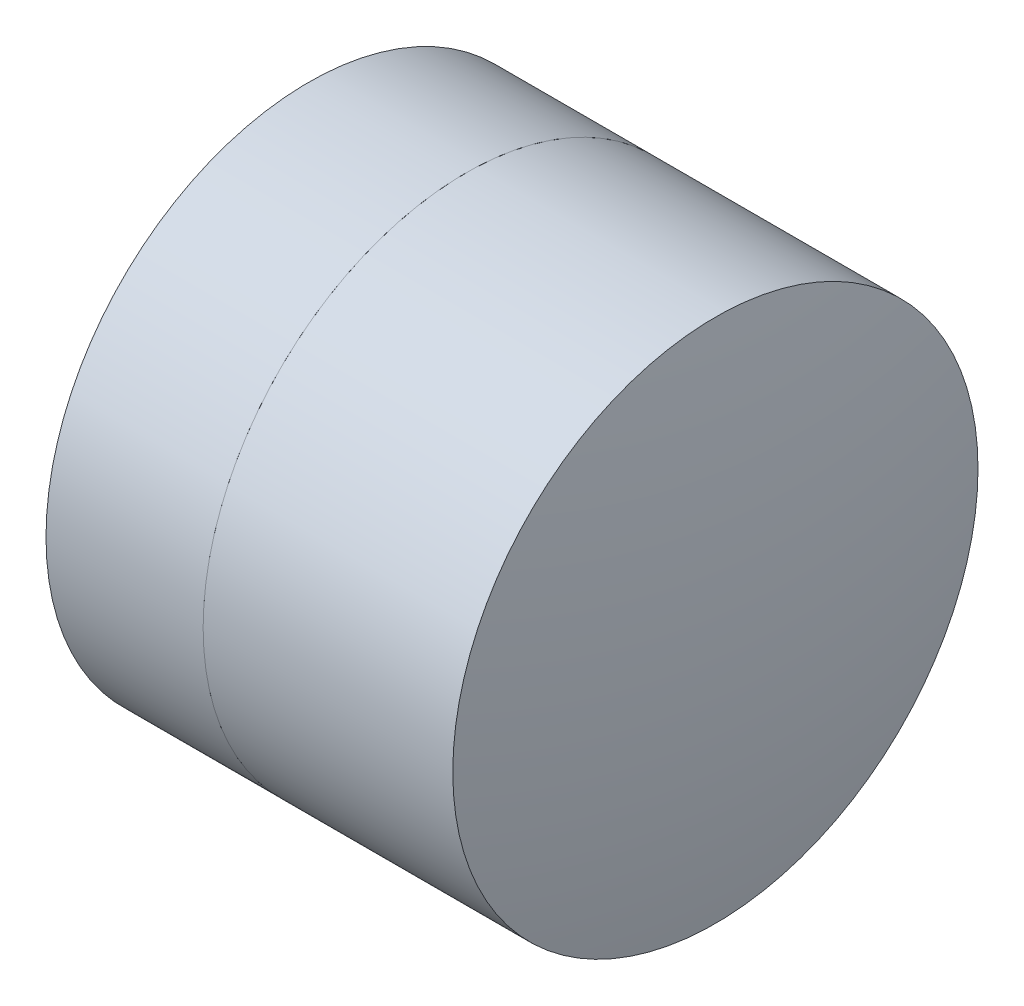
SolidWorks part; units mm, degrees
ref_plane "前视基准面" through (0, 0, 0) normal (0, 0, 1) x (1, 0, 0)
ref_plane "上视基准面" through (0, 0, 0) normal (0, 1, 0) x (1, 0, 0)
ref_plane "右视基准面" through (0, 0, 0) normal (1, 0, 0) x (0, 0, -1)
sketch "草图1" plane through (0, 0, 0) normal (0, 1, 0) x (1, 0, 0)
  line L0 (-0.8161, 0) -> (3.5052, 0) construction
  line L1 (0.3591, -1.5) -> (1.2566, -1.5)
  line L2 (0.3591, 1.5) -> (1.2566, 1.5)
  arc A0 (1.2566, -1.5) -> (1.2566, 1.5) centre (0.1772, 0) ccw
  arc A1 (0.3591, 1.5) -> (0.3591, -1.5) centre (2.7352, 0) ccw
  point P10 (-0.0748, 0)
  point P11 (2.0252, 0)
  dimension "D3" = 2.81
  dimension "D4" = 1.848
  dimension "D1" = 1.5
  dimension "D2" = 1.5
  dimension "D5" = 2.1
revolve "旋转1" add sketch "草图1" angle 360 about L0
sketch "草图2" plane through (0, 0, 0) normal (0, 1, 0) x (1, 0, 0)
  line L0 (-0.5519, 0) -> (2.9438, 0) construction
  line L2 (1.2566, 1.5) -> (2.6826, 1.5)
  line L3 (1.2566, -1.5) -> (2.6826, -1.5)
  arc A0 (2.6826, -1.5) -> (2.6826, 1.5) centre (-5.1348, 0) ccw
  arc A1 (1.2566, -1.5) -> (1.2566, 1.5) centre (0.1772, 0) ccw construction
  arc A2 (1.2566, -1.5) -> (1.2566, 1.5) centre (0.1772, 0) ccw
  point P4 (2.0252, 0)
  point P12 (2.8252, 0)
  dimension "D1" = 7.96
  dimension "D2" = 0.8
revolve "旋转2" add sketch "草图2" angle 360 about L0
